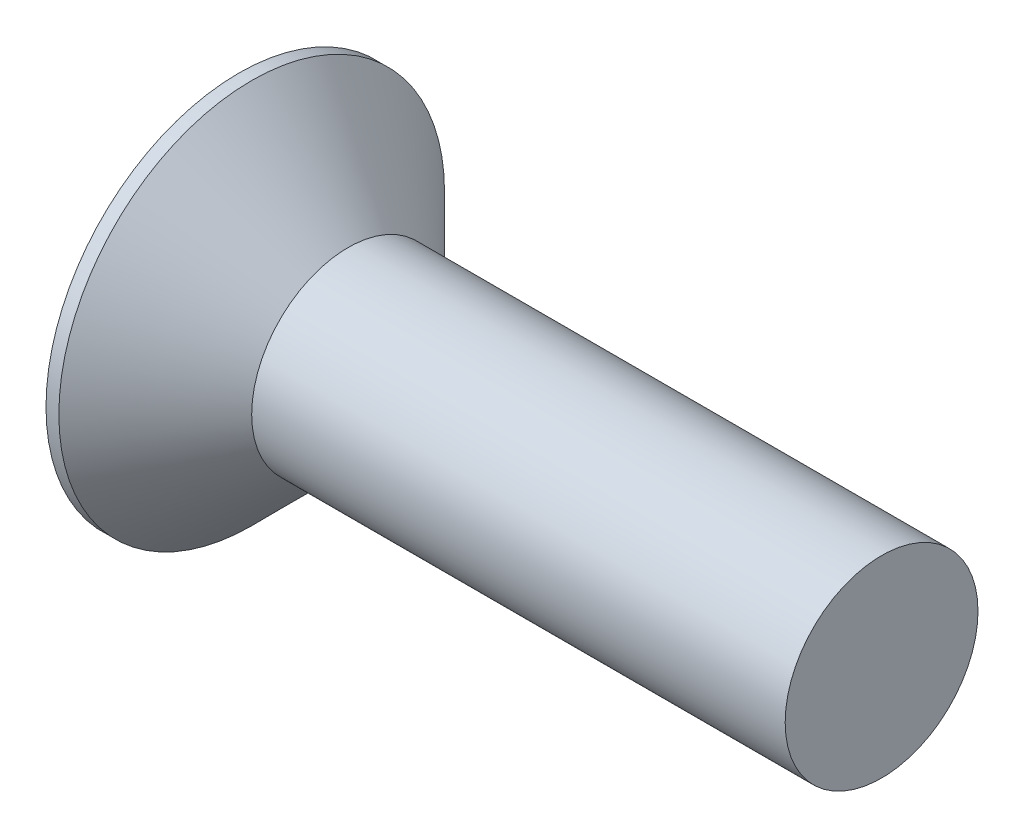
SolidWorks part; units mm, degrees
material "SCM435"
ref_plane "Front Plane" through (0, 0, 0) normal (0, 0, 1) x (1, 0, 0)
ref_plane "Top Plane" through (0, 0, 0) normal (0, 1, 0) x (1, 0, 0)
ref_plane "Right Plane" through (0, 0, 0) normal (1, 0, 0) x (0, 0, -1)
sketch "Sketch1" plane through (0, 0, 0) normal (0, 0, 1) x (1, 0, 0)
  line L0 (-1.7, 0) -> (8.3, 0) construction
  line L1 (-1.7, 0) -> (-1.7, 3)
  line L2 (-1.7, 3) -> (-1.5, 3)
  line L3 (-1.5, 3) -> (0, 1.5)
  line L4 (0, 1.5) -> (8.3, 1.5)
  line L5 (8.3, 1.5) -> (8.3, 0)
  line L6 (-1.7, 0) -> (8.3, 0)
  dimension "A" = 6
  dimension "FIX_1" = 45
  dimension "M" = 3
  dimension "L" = 10
revolve "Revolve1" add sketch "Sketch1" angle 360 about L0
cosmetic thread "ThreadA" parameters "L_s"=8.3, "TD_s"=2.459
sketch "Sketch2" plane through (0, 0, 0) normal (0, 0, 1) x (1, 0, 0)
  line L0 (-0.2491, 0) -> (-0.85, 0) construction
  line L1 (-0.2491, 0) -> (-0.85, 1)
  line L3 (-0.85, 1) -> (-1.7, 1)
  line L4 (-1.7, 0) -> (-0.2491, 0)
  line L6 (-1.7, 0) -> (-1.7, 1)
  dimension "FIX_3" = 59
revolve "Cut-Revolve2" cut sketch "Sketch2" angle 360 about L0
sketch "Sketch3" plane through (-1.7, 0, 0) normal (-1, 0, 0) x (0, 0, 1)
  line L1 (0, 1.1547) -> (-1, 0.5774)
  line L2 (-1, 0.5774) -> (-1, -0.5774)
  line L3 (-1, -0.5774) -> (0, -1.1547)
  line L4 (0, -1.1547) -> (1, -0.5774)
  line L5 (1, -0.5774) -> (1, 0.5774)
  line L6 (1, 0.5774) -> (0, 1.1547)
  circle A0 centre (0, 0) radius 1 construction
extrude "Cut-Extrude1" cut sketch "Sketch3" against normal blind 0.85
